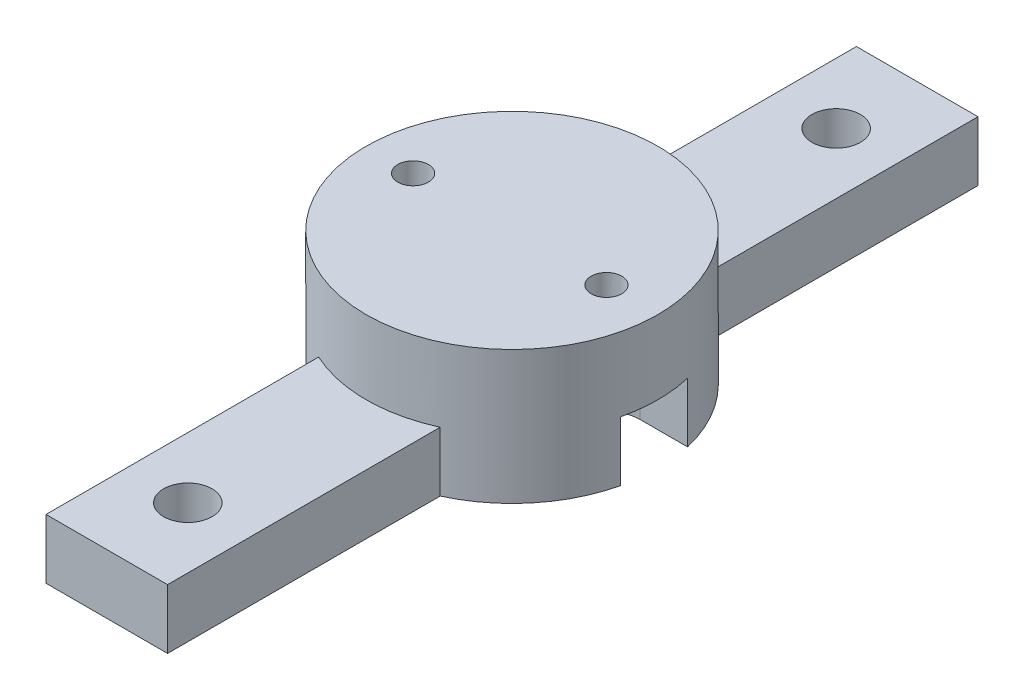
SolidWorks part; units mm, degrees
ref_plane "Front Plane" through (0, 0, 0) normal (0, 0, 1) x (1, 0, 0)
ref_plane "Top Plane" through (0, 0, 0) normal (0, 1, 0) x (1, 0, 0)
ref_plane "Right Plane" through (0, 0, 0) normal (1, 0, 0) x (0, 0, -1)
sketch "Sketch1" plane through (0, 0, 0) normal (0, 1, 0) x (1, 0, 0)
  circle A0 centre (0, 0) radius 11.43
  circle A1 centre (-7.75, 0) radius 1.2
  circle A2 centre (7.4, 0) radius 1.2
  dimension "D1" = 22.86
  dimension "D4" = 2.4
  dimension "D2" = 15.15
  dimension "D3" = 7.75
extrude "Boss-Extrude1" add sketch "Sketch1" along normal blind 5.7785
sketch "Sketch2" plane through (0, 0, 0) normal (0, -1, 0) x (1, 0, 0)
  line L0 (-7.75, -2.9875) -> (-11.0327, -2.9875)
  line L5 (4.7625, -31.75) -> (-4.7625, -31.75)
  line L6 (4.7625, -31.75) -> (4.7625, -10.3905)
  line L7 (4.7625, 31.75) -> (-4.7625, 31.75)
  line L8 (-4.7625, -31.75) -> (-4.7625, -10.3905)
  line L9 (4.7625, -31.75) -> (-4.7625, 31.75) construction
  line L10 (4.7625, 31.75) -> (-4.7625, -31.75) construction
  line L11 (-7.75, 2.9875) -> (-11.0327, 2.9875)
  line L12 (7.4, -2.6375) -> (11.1215, -2.6375)
  line L13 (7.4, 2.6375) -> (11.1215, 2.6375)
  line L14 (-4.7625, 10.3905) -> (-4.7625, 31.75)
  line L15 (4.7625, 10.3905) -> (4.7625, 31.75)
  arc A0 (-11.0327, -2.9875) -> (-4.7625, -10.3905) centre (0, 0) ccw
  arc A1 (-7.75, -2.9875) -> (-7.75, 2.9875) centre (-7.75, 0) ccw
  circle A2 centre (0, 0) radius 11.43
  arc A4 (11.1215, 2.6375) -> (4.7625, 10.3905) centre (0, 0) ccw
  arc A5 (7.4, 2.6375) -> (7.4, -2.6375) centre (7.4, 0) ccw
  arc A6 (4.7625, -10.3905) -> (11.1215, -2.6375) centre (0, 0) ccw
  arc A7 (1.6955, 11.3035) -> (-1.6955, 11.3035) centre (0, 0) ccw construction
  arc A8 (-4.7625, 10.3905) -> (-11.0327, 2.9875) centre (0, 0) ccw
  point P0 (0, 0)
  dimension "D2" = 63.5
  dimension "D1" = 9.525
  dimension "D3" = 0
extrude "Boss-Extrude2" add sketch "Sketch2" along normal offset from surface (4.6716 mm away) 10.4501 up to face at (-7.75, 5.7785, 1.2)
sketch "Sketch3" plane through (0, -4.6716, 0) normal (0, -1, 0) x (1, 0, 0)
  line L0 (0, -25.4) -> (0, 0) construction
  line L1 (0, 0) -> (0, 25.4) construction
  point P0 (0, -25.4)
  point P1 (0, 25.4)
  dimension "D1" = 50.8
hole_wizard "#6 Clearance Hole1" positions "Sketch4" profile "Sketch5" hole size "#6" standard "ANSI Inch" end condition through all
sketch "Sketch4" plane through (0, -4.6716, 0) normal (0, -1, 0) x (-1, 0, 0)
  point P0 (0, 25.4)
  point P3 (0, -25.4)
sketch "Sketch5" plane through (0, -4.6716, -25.4) normal (1, 0, 0) x (0, 0, -1)
  line L0 (0, 0) -> (0, 10.4501)
  line L1 (0, 10.4501) -> (1.8986, 10.4501)
  line L2 (1.8986, 10.4501) -> (1.8986, 0)
  line L5 (1.8986, 0) -> (0, 0)
  line L11 (0, -6.35) -> (0, 107.95) construction
  dimension "Thru Hole Dia." = 3.7973
  dimension "Thru Hole Depth" = 10.4501
